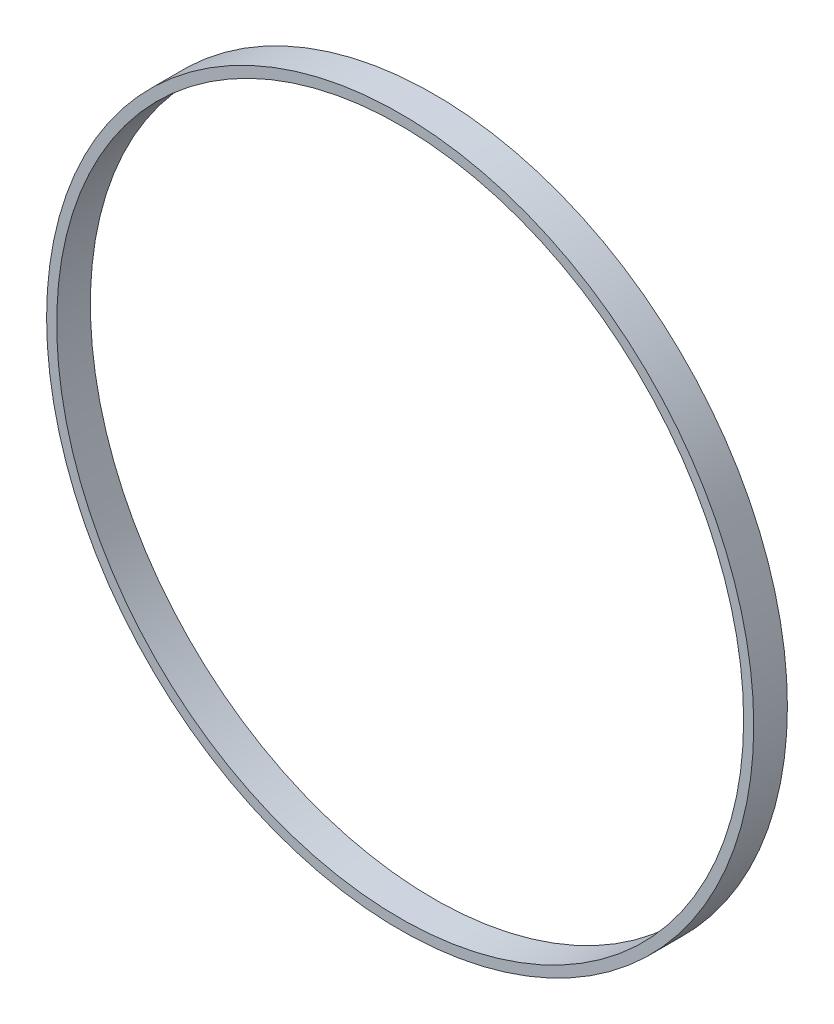
SolidWorks part; units mm, degrees
material "Rubber"
ref_plane "Front Plane" through (0, 0, 0) normal (0, 0, 1) x (1, 0, 0)
ref_plane "Top Plane" through (0, 0, 0) normal (0, 1, 0) x (1, 0, 0)
ref_plane "Right Plane" through (0, 0, 0) normal (1, 0, 0) x (0, 0, -1)
sketch "Sketch1" plane through (0, 0, 0) normal (0, 0, 1) x (1, 0, 0)
  circle A0 centre (0, 0) radius 51
  circle A1 centre (0, 0) radius 52.5
  dimension "D1" = 102
  dimension "D2" = 105
extrude "Boss-Extrude1" add sketch "Sketch1" along normal blind 5
